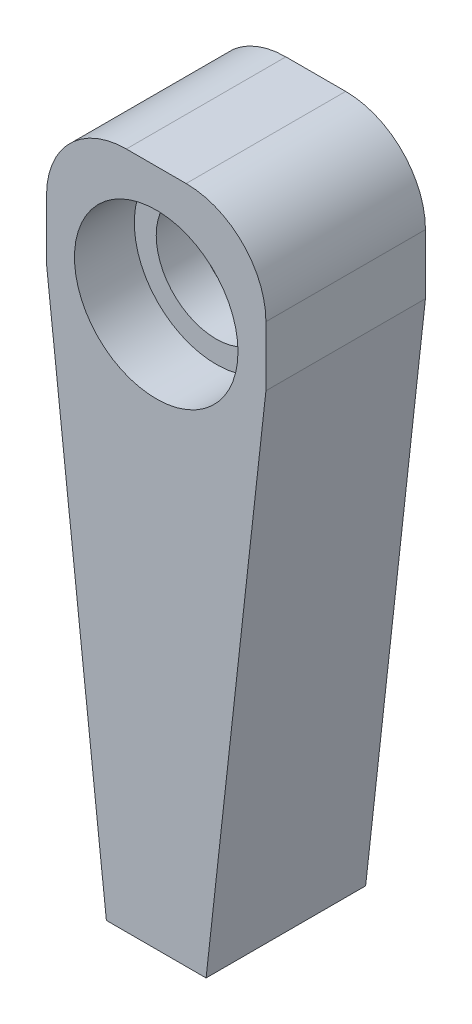
SolidWorks part; units mm, degrees
ref_plane "Спереди" through (0, 0, 0) normal (0, 0, 1) x (1, 0, 0)
ref_plane "Сверху" through (0, 0, 0) normal (0, 1, 0) x (1, 0, 0)
ref_plane "Справа" through (0, 0, 0) normal (1, 0, 0) x (0, 0, -1)
sketch "Эскиз1" plane through (0, 0, 0) normal (0, 1, 0) x (1, 0, 0)
  line L1 (5.5, -4) -> (-5.5, -4)
  line L2 (5.5, -4) -> (5.5, 4)
  line L3 (5.5, 4) -> (-5.5, 4)
  line L4 (-5.5, -4) -> (-5.5, 4)
  line L5 (5.5, -4) -> (-5.5, 4) construction
  line L6 (5.5, 4) -> (-5.5, -4) construction
  point P0 (0, 0)
  dimension "D1" = 11
  dimension "D2" = 8
extrude "Бобышка-Вытянуть1" add sketch "Эскиз1" along normal blind 34
sketch "Эскиз2" plane through (0, 0, -4) normal (0, 0, -1) x (-1, 0, 0)
  line L0 (0, 34) -> (0, 0) construction
  line L1 (-5.5, 34) -> (5.5, 34) construction
  line L2 (-5.5, 0) -> (5.5, 0) construction
  circle A0 centre (0, 28) radius 4.1
  dimension "D1" = 6
extrude "Вырез-Вытянуть1" cut sketch "Эскиз2" against normal blind 3
sketch "Эскиз7" plane through (0, 0, 4) normal (0, 0, 1) x (1, 0, 0)
  line L0 (0, 34) -> (0, 0) construction
  line L1 (-5.5, 34) -> (5.5, 34) construction
  circle A0 centre (0, 28) radius 4.1
  point P5 (0, 34)
  dimension "D1" = 6
sketch "Эскиз4" plane through (0, 0, -1) normal (0, 0, -1) x (-1, 0, 0)
  circle A0 centre (0, 28) radius 3
extrude "Вырез-Вытянуть3" cut sketch "Эскиз4" against normal through all
sketch "Эскиз6" plane through (0, 0, -4) normal (0, 0, -1) x (-1, 0, 0)
  line L0 (-5.5, 27) -> (-2.5, 0)
  line L1 (-5.5, 34) -> (-5.5, 0) construction
  line L2 (-5.5, 0) -> (5.5, 0) construction
  line L3 (-2.5, 0) -> (2.5, 0)
  line L4 (2.5, 0) -> (5.5, 27)
  line L5 (5.5, 34) -> (5.5, 0) construction
  line L6 (5.5, 27) -> (5.5, 34)
  line L7 (5.5, 34) -> (-5.5, 34)
  line L8 (-5.5, 34) -> (-5.5, 27)
  line L9 (-5.5, 34) -> (-5.5, 0) construction
  line L10 (-5.5, 27) -> (5.5, 27) construction
  dimension "D1" = 5
  dimension "D2" = 7
extrude "Вырез-Вытянуть5" cut sketch "Эскиз6" against normal blind 10 flip side to cut
fillet "Скругление1" radius 4 2 edges at (5.5, 34, 0) (-5.5, 34, 0)
sketch "Эскиз5" plane through (0, 0, 0) normal (0, -1, 0) x (1, 0, 0)
  circle A0 centre (0, 0) radius 0.65
extrude "Вырез-Вытянуть4" cut sketch "Эскиз5" against normal blind 20
extrude "Вырез-Вытянуть6" cut sketch "Эскиз7" against normal blind 3
